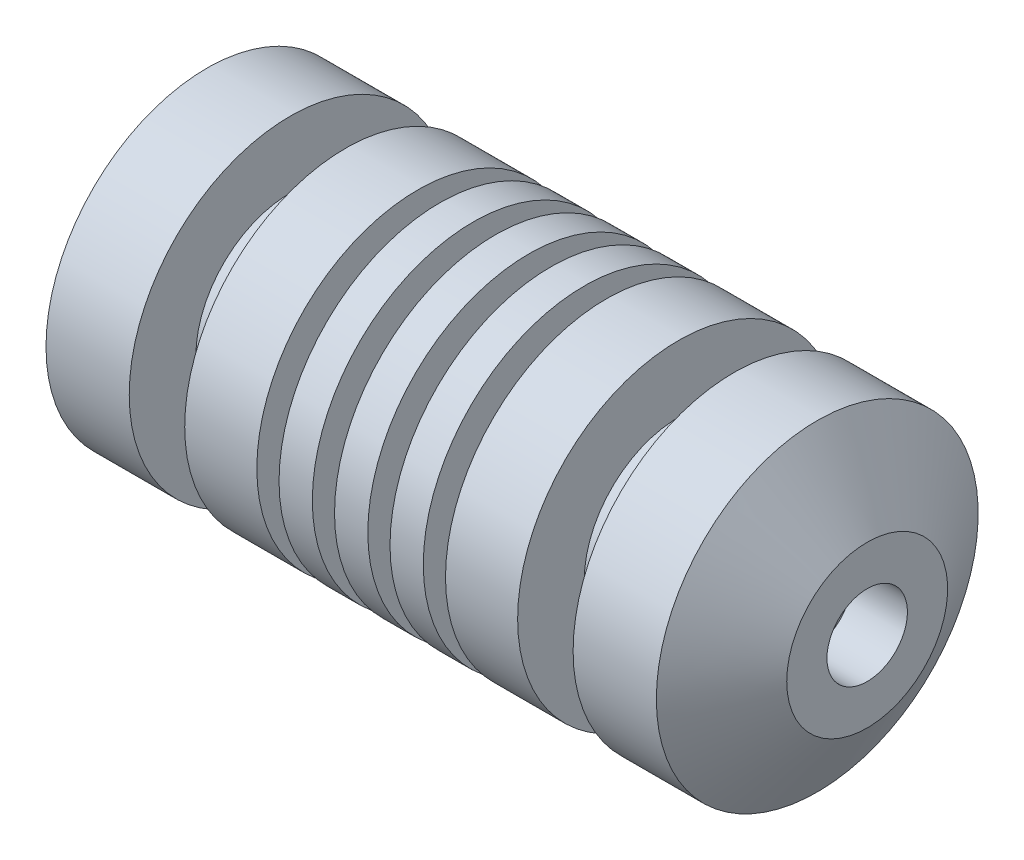
SolidWorks part; units mm, degrees
ref_plane "Front Plane" through (0, 0, 0) normal (0, 0, 1) x (1, 0, 0)
ref_plane "Top Plane" through (0, 0, 0) normal (0, 1, 0) x (1, 0, 0)
ref_plane "Right Plane" through (0, 0, 0) normal (1, 0, 0) x (0, 0, -1)
sketch "Sketch1" plane through (0, 0, 0) normal (0, 0, 1) x (1, 0, 0)
  line L0 (0, 0) -> (113.03, 0)
  line L42 (0, 36.83) -> (19.05, 36.83)
  line L43 (48.26, 36.83) -> (48.26, 29.21)
  line L44 (60.96, 36.83) -> (60.96, 29.21)
  line L45 (19.05, 36.83) -> (19.05, 21.59)
  line L46 (73.66, 36.83) -> (73.66, 29.21)
  line L48 (86.36, 36.83) -> (86.36, 29.21)
  line L49 (107.95, 36.83) -> (107.95, 21.59)
  line L50 (31.75, 36.83) -> (31.75, 21.59)
  line L52 (53.34, 36.83) -> (53.34, 29.21)
  line L53 (139.7, 36.83) -> (151.13, 18.415)
  line L54 (120.65, 36.83) -> (120.65, 21.59)
  line L55 (19.05, 21.59) -> (31.75, 21.59)
  line L56 (66.04, 36.83) -> (66.04, 29.21)
  line L57 (78.74, 36.83) -> (78.74, 29.21)
  line L58 (91.44, 36.83) -> (91.44, 29.21)
  line L59 (48.26, 29.21) -> (53.34, 29.21)
  line L60 (107.95, 21.59) -> (120.65, 21.59)
  line L61 (53.34, 36.83) -> (60.96, 36.83)
  line L62 (60.96, 29.21) -> (66.04, 29.21)
  line L63 (66.04, 36.83) -> (73.66, 36.83)
  line L64 (73.66, 29.21) -> (78.74, 29.21)
  line L65 (78.74, 36.83) -> (86.36, 36.83)
  line L66 (86.36, 29.21) -> (91.44, 29.21)
  line L67 (91.44, 36.83) -> (107.95, 36.83)
  line L68 (31.75, 36.83) -> (48.26, 36.83)
  line L69 (120.65, 36.83) -> (139.7, 36.83)
  line L70 (0, 36.83) -> (0, 0)
  line L74 (151.13, 18.415) -> (151.13, 9.2075)
  line L75 (151.13, 9.2075) -> (138.43, 9.2075)
  line L76 (138.43, 9.2075) -> (138.43, 6.35)
  line L77 (138.43, 6.35) -> (125.73, 6.35)
  line L78 (125.73, 6.35) -> (125.73, 3.81)
  line L79 (125.73, 3.81) -> (113.03, 3.81)
  line L80 (113.03, 3.81) -> (113.03, 0)
  dimension "D4" = 36.83
revolve "Revolve5" add sketch "Sketch1" angle 360 about L0
sketch "Sketch3" plane through (113.03, 0, 0) normal (1, 0, 0) x (0, 0, -1)
  circle A0 centre (0, 0) radius 3.81
extrude "Cut-Extrude1" cut sketch "Sketch3" against normal blind 2.54 draft 56
